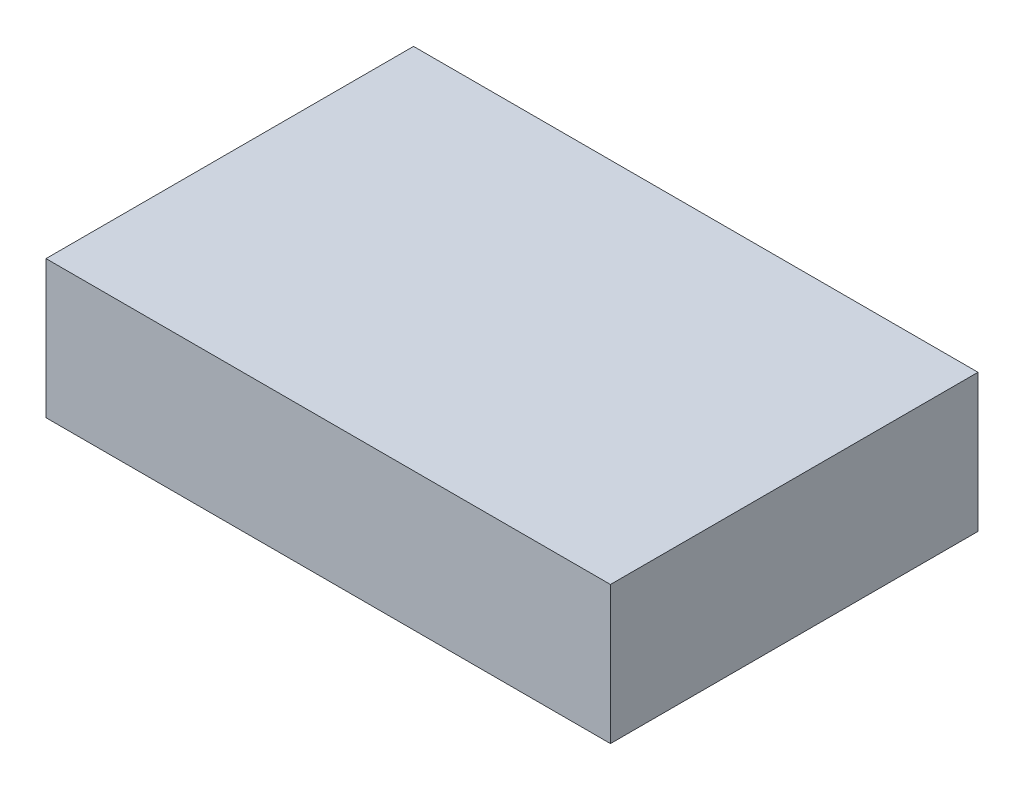
SolidWorks part; units mm, degrees
ref_plane "Front Plane" through (0, 0, 0) normal (0, 0, 1) x (1, 0, 0)
ref_plane "Top Plane" through (0, 0, 0) normal (0, 1, 0) x (1, 0, 0)
ref_plane "Right Plane" through (0, 0, 0) normal (1, 0, 0) x (0, 0, -1)
sketch "Sketch1" plane through (0, 0, 0) normal (0, 1, 0) x (1, 0, 0)
  line L1 (-43, -28) -> (43, -28)
  line L2 (-43, -28) -> (-43, 28)
  line L3 (-43, 28) -> (43, 28)
  line L4 (43, -28) -> (43, 28)
  line L5 (-43, -28) -> (43, 28) construction
  line L6 (-43, 28) -> (43, -28) construction
  point P0 (0, 0)
  dimension "D1" = 86
  dimension "D2" = 56
extrude "Boss-Extrude1" add sketch "Sketch1" along normal blind 21
